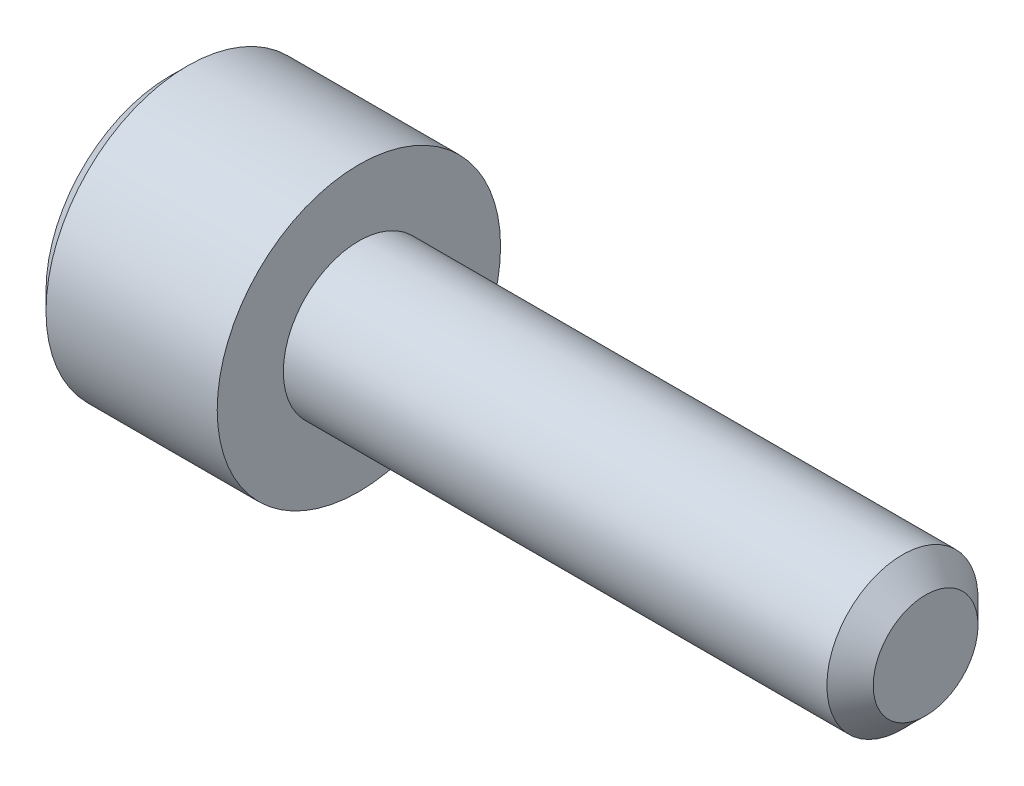
SolidWorks part; units mm, degrees
material "AISI 304"
ref_plane "正面" through (0, 0, 0) normal (0, 0, 1) x (1, 0, 0)
ref_plane "平面" through (0, 0, 0) normal (0, 1, 0) x (1, 0, 0)
ref_plane "右側面" through (0, 0, 0) normal (1, 0, 0) x (0, 0, -1)
ref_plane "Plane1" through (0, 0, 0) normal (0, 0, 1) x (1, 0, 0)
sketch "Sketch1" plane through (0, 0, 0) normal (0, 0, 1) x (1, 0, 0)
  line L0 (-2, 0) -> (-2, 1.3125)
  line L1 (-2, 1.3125) -> (-1.8125, 1.5)
  line L2 (-1.8125, 1.5) -> (0, 1.5)
  line L3 (0, 1.5) -> (0, 0.8)
  line L4 (0, 0.8) -> (5.7545, 0.8)
  line L5 (5.7545, 0.8) -> (6, 0.5545)
  line L6 (6, 0.5545) -> (6, 0)
  line L7 (6, 0) -> (-2, 0)
  line L8 (6, 0) -> (-2, 0) construction
  dimension "D1" = 0.8
revolve "Revolve1" add sketch "Sketch1" angle 360 about L8
cosmetic thread "Cosmetic Thread1" parameters "D1"=5.5, "D2"=1.509
ref_plane "Plane2" through (0, 0, 0) normal (0, 0, 1) x (1, 0, 0)
sketch "Sketch2" plane through (0, 0, 0) normal (0, 0, 1) x (1, 0, 0)
  line L0 (-2, 0) -> (-2, 0.9)
  line L1 (-2, 0.9) -> (-1.85, 0.75)
  line L2 (-1.85, 0.75) -> (-1, 0.75)
  line L3 (-1, 0.75) -> (-0.6, 0)
  line L4 (-0.6, 0) -> (-2, 0)
  line L5 (-0.6, 0) -> (-2, 0) construction
revolve "Cut-Revolve1" cut sketch "Sketch2" angle 360 about L5
ref_plane "Plane3" through (-2, 0, 0) normal (1, 0, 0) x (0, 0, -1)
sketch "Sketch3" plane through (-2, 0, 0) normal (1, 0, 0) x (0, 0, -1)
  line L0 (-0.75, -0.433) -> (0, -0.866)
  line L1 (0, -0.866) -> (0.75, -0.433)
  line L2 (0.75, -0.433) -> (0.75, 0.433)
  line L3 (0.75, 0.433) -> (0, 0.866)
  line L4 (0, 0.866) -> (-0.75, 0.433)
  line L5 (-0.75, 0.433) -> (-0.75, -0.433)
extrude "Cut-Extrude1" cut sketch "Sketch3" along normal blind 1
